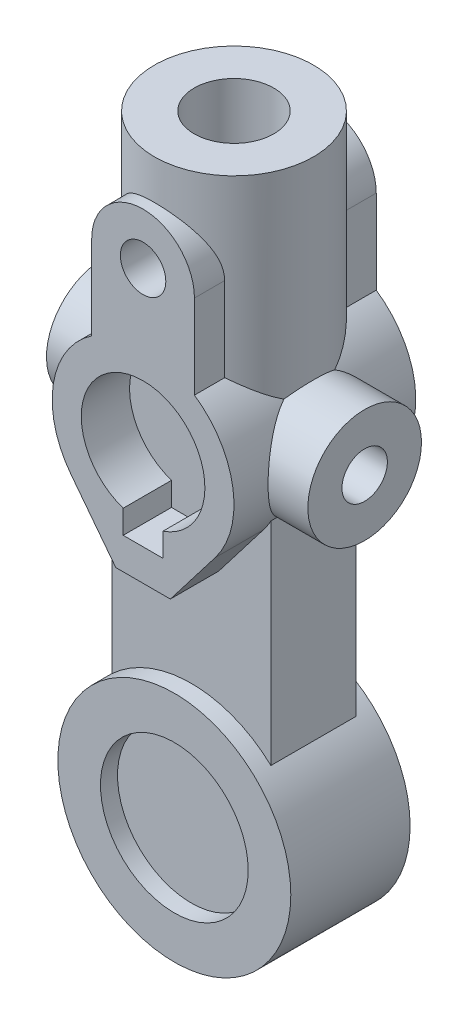
SolidWorks part; units mm, degrees
ref_plane "Alzado" through (0, 0, 0) normal (0, 0, 1) x (1, 0, 0)
ref_plane "Planta" through (0, 0, 0) normal (0, 1, 0) x (1, 0, 0)
ref_plane "Vista lateral" through (0, 0, 0) normal (1, 0, 0) x (0, 0, -1)
sketch "Croquis1" plane through (0, 0, 0) normal (0, 0, 1) x (1, 0, 0)
  line L0 (0, 0) -> (0, 87.0717) construction
  line L1 (-14.351, 44.45) -> (-14.351, 20.9573)
  line L2 (14.351, 44.45) -> (14.351, 20.9573)
  line L3 (0, 0) -> (0, -45.8368) construction
  line L4 (-5.5562, -22.9184) -> (5.5563, -22.9184)
  line L5 (5.5563, -22.9184) -> (5.5562, -16.3539)
  line L6 (-5.5562, -22.9184) -> (-5.5562, -16.3539)
  line L7 (-7.62, -31.75) -> (7.62, -31.75)
  line L8 (7.62, -31.75) -> (20.1312, -15.4885)
  line L9 (-7.62, -31.75) -> (-20.1312, -15.4885)
  arc A0 (5.5562, -16.3539) -> (-5.5562, -16.3539) centre (0, 0) ccw
  arc A1 (-14.351, 20.9573) -> (-20.1312, -15.4885) centre (0, 0) ccw
  circle A2 centre (0, 44.45) radius 6.35
  arc A3 (14.351, 44.45) -> (-14.351, 44.45) centre (0, 44.45) ccw
  arc A4 (20.1312, -15.4885) -> (14.351, 20.9573) centre (0, 0) ccw
  point P1 (0, 0)
  point P14 (0, -22.9184)
  point P17 (0, -31.75)
  point P21 (0, 0)
  dimension "D1" = 12.7
  dimension "D2" = 28.702
  dimension "D3" = 50.8
  dimension "D4" = 34.544
  dimension "D5" = 44.45
  dimension "D6" = 11.1125
  dimension "D7" = 22.9184
  dimension "D8" = 15.24
  dimension "D9" = 31.75
extrude "Saliente-Extruir1" add sketch "Croquis1" along normal mid plane 50.8
ref_plane "Plano1" through (0, 69.85, 0) normal (0, 1, 0) x (1, 0, 0)
sketch "Croquis2" plane through (0, 69.85, 0) normal (0, 1, 0) x (1, 0, 0)
  circle A0 centre (0, 0) radius 11.1125
  circle A1 centre (0, 0) radius 22.225
  dimension "D1" = 44.45
  dimension "D2" = 22.225
extrude "Saliente-Extruir2" add sketch "Croquis2" against normal up to next
sketch "Croquis3" plane through (0, 69.85, 0) normal (0, 1, 0) x (1, 0, 0)
  circle A0 centre (0, 0) radius 11.1125
  dimension "D1" = 22.225
extrude "Cortar-Extruir1" cut sketch "Croquis3" against normal up to surface (52.578 mm away)
sketch "Croquis4" plane through (0, 0, 0) normal (0, 0, 1) x (1, 0, 0)
  line L0 (0, 0) -> (0, -121.6733) construction
  circle A0 centre (0, -95.25) radius 20.6375
  circle A1 centre (0, -95.25) radius 32.5437
  dimension "D1" = 65.0875
  dimension "D2" = 41.275
  dimension "D3" = 95.25
extrude "Saliente-Extruir3" add sketch "Croquis4" along normal mid plane 33.3375 separate body
sketch "Croquis5" plane through (0, 0, 0) normal (0, 0, 1) x (1, 0, 0)
  line L0 (0, 0) -> (0, -95.25) construction
  line L1 (-22.225, -12.2967) -> (-22.225, -71.4772)
  line L2 (22.225, -12.2967) -> (22.225, -71.4772)
  line L4 (22.225, 0) -> (22.225, -95.25) construction
  line L5 (-22.225, 0) -> (-22.225, -95.25) construction
  arc A0 (-22.225, -71.4772) -> (22.225, -71.4772) centre (0, -95.25) ccw
  arc A1 (22.225, -12.2967) -> (-22.225, -12.2967) centre (0, 0) ccw
  dimension "D1" = 50.8
  dimension "D2" = 65.0875
  dimension "D3" = 22.225
  dimension "D4" = 22.225
extrude "Saliente-Extruir4" add sketch "Croquis5" along normal mid plane 23.8125
ref_plane "Plano2" through (36.5125, 0, 0) normal (1, 0, 0) x (0, 0, -1)
sketch "Croquis6" plane through (36.5125, 0, 0) normal (1, 0, 0) x (0, 0, -1)
  circle A0 centre (0, 0) radius 6.35
  circle A1 centre (0, 0) radius 15.875
  dimension "D1" = 12.7
  dimension "D2" = 31.75
extrude "Saliente-Extruir5" add sketch "Croquis6" against normal up to next
sketch "Croquis7" plane through (36.5125, 0, 0) normal (1, 0, 0) x (0, 0, -1)
  circle A0 centre (0, 0) radius 6.35
  dimension "D1" = 12.7
extrude "Cortar-Extruir4" cut sketch "Croquis7" against normal up to surface (11.1125 mm away)
mirror "Simetría1" about plane through (0, 0, 0) normal (1, 0, 0) of "Saliente-Extruir5", "Cortar-Extruir4"
